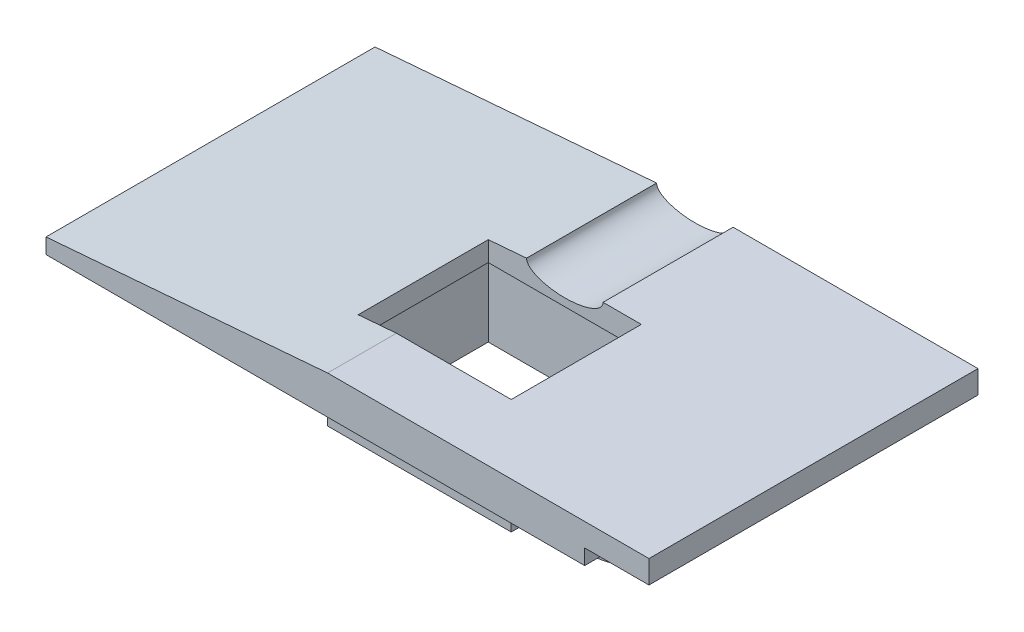
SolidWorks part; units mm, degrees
ref_plane "Alzado" through (0, 0, 0) normal (0, 0, 1) x (1, 0, 0)
ref_plane "Planta" through (0, 0, 0) normal (0, 1, 0) x (1, 0, 0)
ref_plane "Vista lateral" through (0, 0, 0) normal (1, 0, 0) x (0, 0, -1)
sketch "Croquis1" plane through (0, 0, 0) normal (0, 0, 1) x (1, 0, 0)
  line L0 (-7.839, 5.1692) -> (13.161, 5.1692)
  line L1 (13.161, 5.1692) -> (13.161, 3.6692)
  line L2 (13.161, 3.6692) -> (8.961, 3.6692)
  line L3 (8.961, 3.6692) -> (8.961, 2.6692)
  line L4 (8.961, 2.6692) -> (-26.239, 2.6692)
  line L5 (-26.239, 2.6692) -> (-26.239, 3.6692)
  line L6 (-26.239, 3.6692) -> (-7.839, 5.1692)
  dimension "D1" = 21
  dimension "D2" = 1.5
  dimension "D3" = 4.2
  dimension "D4" = 1
  dimension "D5" = 35.2
extrude "Saliente-Extruir1" add sketch "Croquis1" along normal blind 21.5 contours L6 L0 L1 L2 L3 L4 L5
sketch "Croquis2" plane through (0, 0, 0) normal (0, 0, -1) x (-1, 0, 0)
  line L0 (7.839, 5.1692) -> (5.339, 5.1692) construction
  line L1 (7.839, 5.1692) -> (-13.161, 5.1692) construction
  line L2 (2.839, 5.1692) -> (7.839, 5.1692)
  ellipse E0 centre (5.339, 5.1692) end of major axis (7.839, 5.1692) minor radius 1 (5.339, 4.1692) -> (7.839, 5.1692) ccw
  ellipse E1 centre (5.339, 5.1692) end of major axis (2.839, 5.1692) minor radius 1 (5.339, 4.1692) -> (2.839, 5.1692) cw
extrude "Cortar-Extruir1" cut sketch "Croquis2" against normal blind 8.5
sketch "Croquis3" plane through (0, 5.1692, 0) normal (0, 1, 0) x (1, 0, 0)
  line L0 (-5.339, -8.5) -> (-10.339, -8.5)
  line L1 (-7.839, -8.5) -> (-2.839, -8.5) construction
  line L2 (-10.339, -8.5) -> (-10.339, -17)
  line L3 (-10.339, -17) -> (-0.339, -17)
  line L4 (-0.339, -17) -> (-0.339, -8.5)
  line L5 (-0.339, -8.5) -> (-5.339, -8.5)
extrude "Cortar-Extruir2" cut sketch "Croquis3" against normal through all
sketch "Croquis5" plane through (0, 2.6692, 0) normal (0, -1, 0) x (1, 0, 0)
  line L0 (-10.339, 17) -> (-10.339, 8.5) construction
  line L1 (-10.339, 8.5) -> (-0.339, 8.5) construction
  line L2 (-0.339, 8.5) -> (-0.339, 17) construction
  line L3 (-0.339, 17) -> (-10.339, 17) construction
  line L4 (-10.339, 12.75) -> (-0.339, 12.75) construction
  line L5 (-5.339, 17) -> (-5.339, 8.5) construction
  line L6 (-11.339, 18) -> (-11.339, 7.5)
  line L8 (0.661, 7.5) -> (0.661, 18)
  line L9 (0.661, 18) -> (-11.339, 18)
  line L10 (-11.339, 7.5) -> (0.661, 7.5)
  dimension "D1" = 1
  dimension "D2" = 1
  dimension "D3" = 1
  dimension "D4" = 1
extrude "Saliente-Extruir2" add sketch "Croquis5" along normal blind 4
sketch "Croquis6" plane through (0, -1.3308, 0) normal (0, -1, 0) x (1, 0, 0)
  line L8 (0.161, 17.5) -> (-10.839, 17.5)
  line L9 (-10.839, 17.5) -> (-10.839, 8)
  line L10 (-10.839, 8) -> (0.161, 8)
  line L11 (0.161, 8) -> (0.161, 17.5)
  line L12 (0.161, 17.5) -> (-10.839, 17.5)
  line L13 (-10.839, 17.5) -> (-10.839, 8)
  line L14 (-10.839, 8) -> (0.161, 8)
  line L15 (0.161, 8) -> (0.161, 17.5)
  dimension "D1" = 0.5
extrude "Cortar-Extruir3" cut sketch "Croquis6" against normal blind 5
sketch "Croquis7" plane through (0, 2.6692, 0) normal (0, -1, 0) x (1, 0, 0)
  line L0 (0.661, 18) -> (0.661, 7.5) construction
  line L1 (8.961, 18) -> (8.961, 7.5) construction
  line L2 (8.961, 21.5) -> (8.961, 0) construction
  line L3 (8.961, 21.5) -> (8.961, 0) construction
sketch "Croquis8" plane through (0, 2.6692, 0) normal (0, -1, 0) x (1, 0, 0)
  line L0 (0.661, 18) -> (0.661, 7.5) construction
  line L1 (0.661, 12.75) -> (8.961, 12.75) construction
  line L2 (8.961, 18) -> (8.961, 7.5) construction
  circle A2 centre (3.561, 12.75) radius 2.95
  dimension "D1" = 5.9
  dimension "D2" = 2.9
  dimension "D3" = 0
extrude "Saliente-Extruir8" add sketch "Croquis8" along normal blind 5
sketch "Croquis9" plane through (0, -2.3308, 0) normal (0, -1, 0) x (1, 0, 0)
  circle A2 centre (3.561, 12.75) radius 0.95
  circle A3 centre (3.561, 12.75) radius 0.95
  dimension "D1" = 2
extrude "Cortar-Extruir4" cut sketch "Croquis9" against normal blind 5.5
sketch "Croquis12" plane through (0, 2.6692, 0) normal (0, -1, 0) x (1, 0, 0)
  line L0 (-11.339, 18) -> (-11.339, 7.5) construction
  line L1 (-14.249, 12.75) -> (-11.339, 12.75) construction
  line L2 (-11.339, 18) -> (-11.339, 7.5) construction
  circle A0 centre (-14.249, 12.75) radius 2.9
  dimension "D1" = 2.91
  dimension "D2" = 90
extrude "Saliente-Extruir14" add sketch "Croquis12" along normal blind 5
sketch "Croquis13" plane through (0, -2.3308, 0) normal (0, -1, 0) x (1, 0, 0)
  circle A2 centre (-14.249, 12.75) radius 0.9
  circle A3 centre (-14.249, 12.75) radius 0.9
  dimension "D1" = 2
extrude "Cortar-Extruir5" cut sketch "Croquis13" against normal blind 5.5
